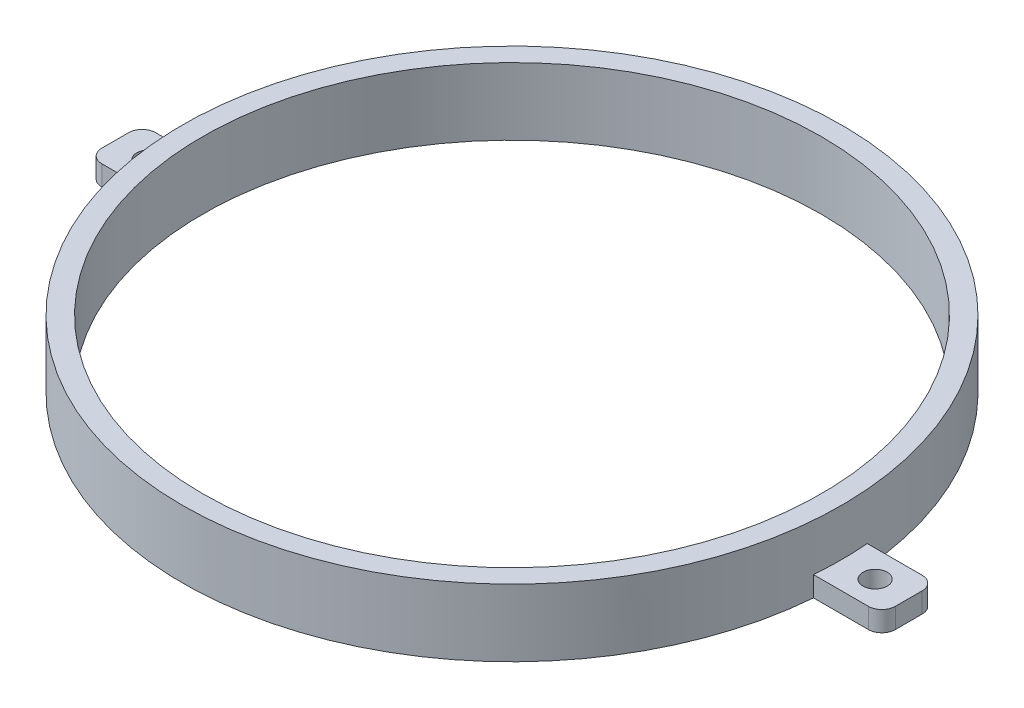
SolidWorks part; units mm, degrees
ref_plane "Front Plane" through (0, 0, 0) normal (0, 0, 1) x (1, 0, 0)
ref_plane "Top Plane" through (0, 0, 0) normal (0, 1, 0) x (1, 0, 0)
ref_plane "Right Plane" through (0, 0, 0) normal (1, 0, 0) x (0, 0, -1)
sketch "Sketch1" plane through (0, 0, 0) normal (0, 1, 0) x (1, 0, 0)
  circle A0 centre (0, 0) radius 46
  circle A1 centre (0, 0) radius 49
  dimension "D1" = 92
  dimension "D2" = 3
extrude "Boss-Extrude1" add sketch "Sketch1" along normal blind 10
sketch "Sketch2" plane through (0, 0, 0) normal (0, 1, 0) x (1, 0, 0)
  line L0 (0, 0) -> (-82.1712, 0) construction
  line L1 (-46, 0) -> (-46, 4)
  line L2 (-46, 4) -> (-57, 4)
  line L3 (-59, 2) -> (-59, -2)
  line L4 (-57, -4) -> (-46, -4)
  line L5 (-46, -4) -> (-46, 0)
  circle A0 centre (0, 0) radius 46 construction
  circle A1 centre (0, 0) radius 46 construction
  circle A2 centre (-54, 0) radius 1.8
  arc A3 (-59, 2) -> (-57, 4) centre (-57, 2) cw
  arc A4 (-57, -4) -> (-59, -2) centre (-57, -2) cw
  dimension "D3" = 3.6
  dimension "D5" = 2
  dimension "D6" = 2
  dimension "D1" = 8
  dimension "D2" = 13
  dimension "D4" = 8
extrude "Boss-Extrude2" add sketch "Sketch2" along normal blind 3
mirror "Mirror1" about plane through (0, 0, 0) normal (1, 0, 0) of "Boss-Extrude2"
